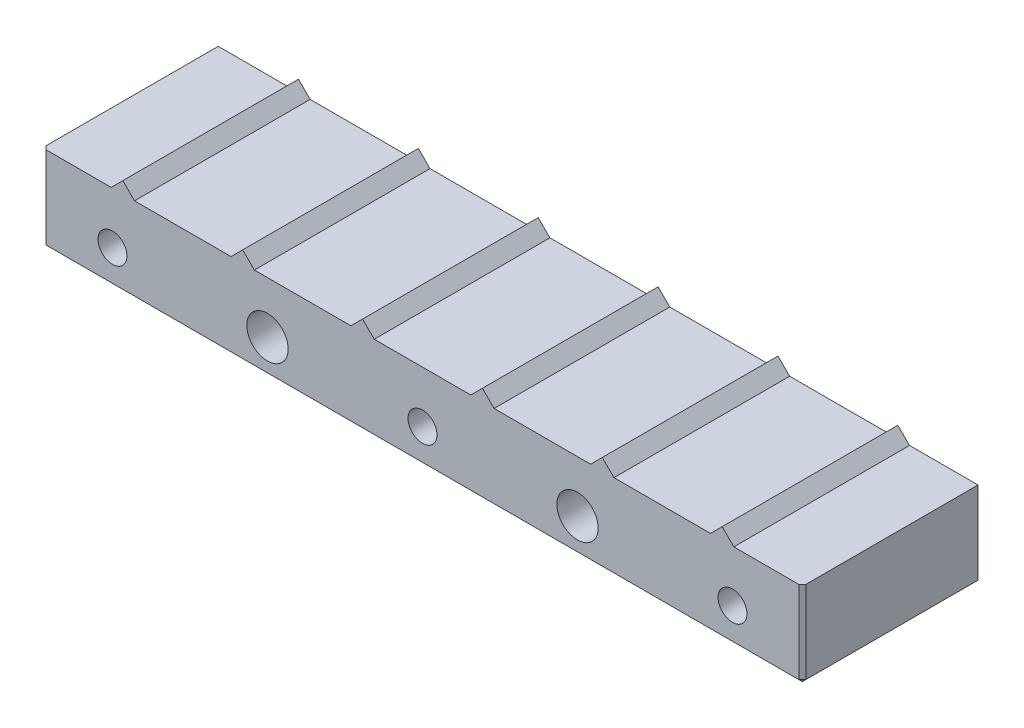
SolidWorks part; units mm, degrees
ref_plane "Спереди" through (0, 0, 0) normal (0, 0, 1) x (1, 0, 0)
ref_plane "Сверху" through (0, 0, 0) normal (0, 1, 0) x (1, 0, 0)
ref_plane "Справа" through (0, 0, 0) normal (1, 0, 0) x (0, 0, -1)
sketch "Эскиз1" plane through (0, 0, 0) normal (0, 0, 1) x (1, 0, 0)
  line L0 (110.285, 12.475) -> (110.285, 0)
  line L1 (100.3438, 12.475) -> (110.285, 12.475)
  line L2 (98.65, 14.1688) -> (100.3438, 12.475)
  line L3 (0, 0) -> (0, 12.475)
  line L4 (0, 0) -> (110.285, 0)
  line L5 (96.9562, 12.475) -> (98.65, 14.1688)
  line L6 (82.9438, 12.475) -> (96.9562, 12.475)
  line L7 (81.25, 14.1688) -> (82.9438, 12.475)
  line L8 (79.5562, 12.475) -> (81.25, 14.1688)
  line L9 (65.5438, 12.475) -> (79.5562, 12.475)
  line L10 (63.85, 14.1688) -> (65.5438, 12.475)
  line L11 (62.1562, 12.475) -> (63.85, 14.1688)
  line L12 (48.1438, 12.475) -> (62.1562, 12.475)
  line L13 (46.45, 14.1688) -> (48.1438, 12.475)
  line L14 (44.7562, 12.475) -> (46.45, 14.1688)
  line L15 (30.7438, 12.475) -> (44.7562, 12.475)
  line L16 (29.05, 14.1688) -> (30.7438, 12.475)
  line L17 (27.3562, 12.475) -> (29.05, 14.1688)
  line L18 (13.3438, 12.475) -> (27.3562, 12.475)
  line L19 (11.65, 14.1688) -> (13.3438, 12.475)
  line L20 (9.9562, 12.475) -> (11.65, 14.1688)
  line L21 (9.9562, 12.475) -> (0, 12.475)
  line L22 (55.15, 31.921) -> (55.15, -19.0092) construction
  line L23 (-19.6044, 4.99) -> (114.3533, 4.99) construction
  line L24 (32.65, 37.161) -> (32.65, -13.7692) construction
  line L25 (77.65, 37.161) -> (77.65, -13.7692) construction
  line L26 (10.15, 37.161) -> (10.15, -13.7692) construction
  line L27 (100.15, 37.161) -> (100.15, -13.7692) construction
  point P25 (55.15, 12.475)
  dimension "D2" = 90
  dimension "D3" = 1.6938
  dimension "D4" = 9.9562
  dimension "D5" = 4.99
  dimension "D6" = 9.9412
  dimension "D7" = 17.4
  dimension "D8" = 45
  dimension "D9" = 7.485
  dimension "D10" = 110.285
  dimension "D12" = 90
  dimension "D13" = 12.475
extrude "Бобышка-Вытянуть1" add sketch "Эскиз1" against normal blind 25.5 contours L21 L3 L4 L0 L1 L2 L5 L6 L7 L8 L9 L10 L11 L12 L13 L14 L15 L16 L17 L18 L19 L20
hole_wizard "Отверстие обработанное метчиком M5x0.81" positions "Эскиз3" profile "Эскиз5" tap size "M5x0.8" standard "Ansi Metric" end condition through all
sketch "Эскиз3" plane through (-77.7293, 6.8084, 0) normal (0, 0, 1) x (1, 0, 0)
  line L23 (177.8793, 30.3526) -> (177.8793, -20.5776) construction
  line L24 (58.1248, -1.8184) -> (192.0826, -1.8184) construction
  line L25 (132.8793, 25.1126) -> (132.8793, -25.8176) construction
  line L26 (87.8793, 30.3526) -> (87.8793, -20.5776) construction
  point P0 (132.8793, -1.8184)
  point P2 (87.8793, -1.8184)
  point P4 (177.8793, -1.8184)
sketch "Эскиз5" plane through (55.15, 4.99, 0) normal (1, 0, 0) x (0, -1, 0)
  line L0 (0, 0) -> (0, 25.5)
  line L1 (0, 25.5) -> (2.1, 25.5)
  line L2 (2.1, 25.5) -> (2.1, 0)
  line L5 (2.1, 0) -> (0, 0)
  line L11 (0, -6.35) -> (0, 107.95) construction
  dimension "Диаметр проходного сверла" = 4.2
  dimension "Глубина проходного сверла" = 25.5
cosmetic thread "Отверстие резьбы1" parameters "D2"=5
cosmetic thread "Отверстие резьбы3" parameters "D2"=5
cosmetic thread "Отверстие резьбы4" parameters "D2"=5
hole_wizard "Отверстия под штифты Ø6.0 мм1" positions "Эскиз6" profile "Эскиз7" hole size "Ø6.0" standard "Ansi Metric" end condition through all
sketch "Эскиз6" plane through (0, 0, 0) normal (0, 0, 1) x (1, 0, 0)
  line L25 (77.65, 37.161) -> (77.65, -13.7692) construction
  line L26 (-19.6044, 4.99) -> (114.3533, 4.99) construction
  line L27 (32.65, 37.161) -> (32.65, -13.7692) construction
  point P0 (32.65, 4.99)
  point P2 (77.65, 4.99)
sketch "Эскиз7" plane through (32.65, 4.99, 0) normal (1, 0, 0) x (0, -1, 0)
  line L0 (0, 0) -> (0, 25.5)
  line L1 (0, 25.5) -> (3, 25.5)
  line L2 (3, 25.5) -> (3, 0)
  line L5 (3, 0) -> (0, 0)
  line L11 (0, -6.35) -> (0, 107.95) construction
  dimension "Диаметр сквозного отверстия" = 6
  dimension "Глубина сквозного отверстия" = 25.5
chamfer "Фаска1" distance 0.5 angle 45 6 edges at (55.1425, 0, -25.5) (0, 0, -12.75) (110.285, 6.2375, 0) (110.285, 0, -12.75) (0, 6.2375, 0) (55.1425, 0, 0)
